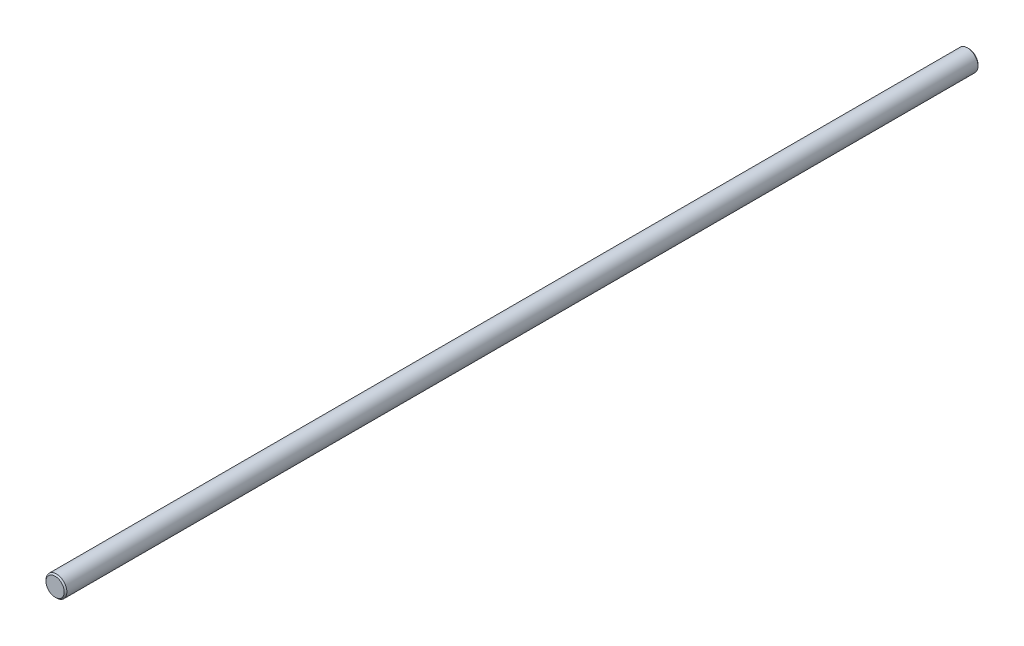
SolidWorks part; units mm, degrees
material "AISI 304"
ref_plane "Front Plane" through (0, 0, 0) normal (0, 0, 1) x (1, 0, 0)
ref_plane "Top Plane" through (0, 0, 0) normal (0, 1, 0) x (1, 0, 0)
ref_plane "Right Plane" through (0, 0, 0) normal (1, 0, 0) x (0, 0, -1)
sketch "Sketch1" plane through (0, 0, 0) normal (0, 0, 1) x (1, 0, 0)
  circle A0 centre (0, 0) radius 4
  dimension "D1" = 8
extrude "Boss-Extrude1" add sketch "Sketch1" against normal blind 350
chamfer "Chamfer1" distance 0.5 angle 45 2 edges at (4, 0, -350) (4, 0, 0)
